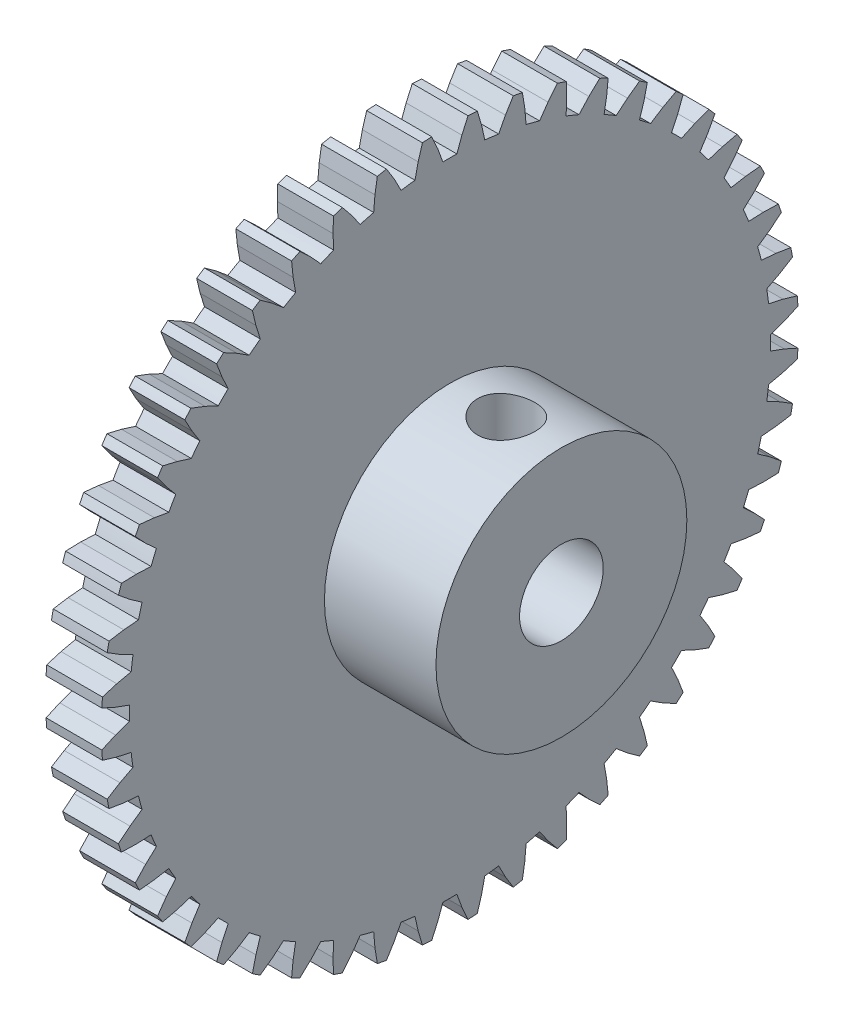
SolidWorks part; units mm, degrees
material "Plain Carbon Steel"
ref_plane "Front Plane" through (0, 0, 0) normal (0, 0, 1) x (1, 0, 0)
ref_plane "Top Plane" through (0, 0, 0) normal (0, 1, 0) x (1, 0, 0)
ref_plane "Right Plane" through (0, 0, 0) normal (1, 0, 0) x (0, 0, -1)
ref_plane "Plane1" through (2, 0, 0) normal (1, 0, 0) x (0, 0, -1)
sketch "Sketch1" plane through (2, 0, 0) normal (1, 0, 0) x (0, 0, -1)
  line L0 (-11.4973, -0.2509) -> (-11.9923, -0.431)
  line L1 (-11.9923, -0.431) -> (-12.483, -0.6512)
  line L2 (-12.4612, -0.9838) -> (-11.9459, -1.138)
  line L3 (-11.9459, -1.138) -> (-11.4316, -1.252)
  line L4 (-11.3662, -1.7494) -> (-11.8334, -1.9926)
  line L5 (-11.8334, -1.9926) -> (-12.2912, -2.2749)
  line L6 (-12.2262, -2.6019) -> (-11.6952, -2.6875)
  line L7 (-11.6952, -2.6875) -> (-11.1704, -2.7334)
  line L8 (-11.0406, -3.218) -> (-11.4721, -3.5202)
  line L9 (-11.4721, -3.5202) -> (-11.8891, -3.8598)
  line L10 (-11.782, -4.1755) -> (-11.2443, -4.191)
  line L11 (-11.2443, -4.191) -> (-10.7181, -4.168)
  line L12 (-10.5261, -4.6316) -> (-10.9145, -4.9875)
  line L13 (-10.9145, -4.9875) -> (-11.2836, -5.3786)
  line L14 (-11.1362, -5.6776) -> (-10.6011, -5.6228)
  line L15 (-10.6011, -5.6228) -> (-10.0824, -5.5314)
  line L16 (-9.8315, -5.9659) -> (-10.1701, -6.3694)
  line L17 (-10.1701, -6.3694) -> (-10.485, -6.8054)
  line L18 (-10.2999, -7.0826) -> (-9.7765, -6.9585)
  line L19 (-9.7765, -6.9585) -> (-9.2741, -6.8001)
  line L20 (-8.9687, -7.1981) -> (-9.2517, -7.6424)
  line L21 (-9.2517, -7.6424) -> (-9.5071, -8.1158)
  line L22 (-9.2873, -8.3664) -> (-8.7846, -8.175)
  line L23 (-8.7846, -8.175) -> (-8.3072, -7.9524)
  line L24 (-7.9524, -8.3072) -> (-8.175, -8.7846)
  line L25 (-8.175, -8.7846) -> (-8.3664, -9.2873)
  line L26 (-8.1158, -9.5071) -> (-7.6424, -9.2517)
  line L27 (-7.6424, -9.2517) -> (-7.1981, -8.9687)
  line L28 (-6.8001, -9.2741) -> (-6.9585, -9.7765)
  line L29 (-6.9585, -9.7765) -> (-7.0826, -10.2999)
  line L30 (-6.8054, -10.485) -> (-6.3694, -10.1701)
  line L31 (-6.3694, -10.1701) -> (-5.9659, -9.8315)
  line L32 (-5.5314, -10.0824) -> (-5.6228, -10.6011)
  line L33 (-5.6228, -10.6011) -> (-5.6776, -11.1362)
  line L34 (-5.3786, -11.2836) -> (-4.9875, -10.9145)
  line L35 (-4.9875, -10.9145) -> (-4.6316, -10.5261)
  line L36 (-4.168, -10.7181) -> (-4.191, -11.2443)
  line L37 (-4.191, -11.2443) -> (-4.1755, -11.782)
  line L38 (-3.8598, -11.8891) -> (-3.5202, -11.4721)
  line L39 (-3.5202, -11.4721) -> (-3.218, -11.0406)
  line L40 (-2.7334, -11.1704) -> (-2.6875, -11.6952)
  line L41 (-2.6875, -11.6952) -> (-2.6019, -12.2262)
  line L42 (-2.2749, -12.2912) -> (-1.9926, -11.8334)
  line L43 (-1.9926, -11.8334) -> (-1.7494, -11.3662)
  line L44 (-1.252, -11.4316) -> (-1.138, -11.9459)
  line L45 (-1.138, -11.9459) -> (-0.9838, -12.4612)
  line L46 (-0.6512, -12.483) -> (-0.431, -11.9923)
  line L47 (-0.431, -11.9923) -> (-0.2509, -11.4973)
  line L48 (0.2509, -11.4973) -> (0.431, -11.9923)
  line L49 (0.431, -11.9923) -> (0.6512, -12.483)
  line L50 (0.9838, -12.4612) -> (1.138, -11.9459)
  line L51 (1.138, -11.9459) -> (1.252, -11.4316)
  line L52 (1.7494, -11.3662) -> (1.9926, -11.8334)
  line L53 (1.9926, -11.8334) -> (2.2749, -12.2912)
  line L54 (2.6019, -12.2262) -> (2.6875, -11.6952)
  line L55 (2.6875, -11.6952) -> (2.7334, -11.1704)
  line L56 (3.218, -11.0406) -> (3.5202, -11.4721)
  line L57 (3.5202, -11.4721) -> (3.8598, -11.8891)
  line L58 (4.1755, -11.782) -> (4.191, -11.2443)
  line L59 (4.191, -11.2443) -> (4.168, -10.7181)
  line L60 (4.6316, -10.5261) -> (4.9875, -10.9145)
  line L61 (4.9875, -10.9145) -> (5.3786, -11.2836)
  line L62 (5.6776, -11.1362) -> (5.6228, -10.6011)
  line L63 (5.6228, -10.6011) -> (5.5314, -10.0824)
  line L64 (5.9659, -9.8315) -> (6.3694, -10.1701)
  line L65 (6.3694, -10.1701) -> (6.8054, -10.485)
  line L66 (7.0826, -10.2999) -> (6.9585, -9.7765)
  line L67 (6.9585, -9.7765) -> (6.8001, -9.2741)
  line L68 (7.1981, -8.9687) -> (7.6424, -9.2517)
  line L69 (7.6424, -9.2517) -> (8.1158, -9.5071)
  line L70 (8.3664, -9.2873) -> (8.175, -8.7846)
  line L71 (8.175, -8.7846) -> (7.9524, -8.3072)
  line L72 (8.3072, -7.9524) -> (8.7846, -8.175)
  line L73 (8.7846, -8.175) -> (9.2873, -8.3664)
  line L74 (9.5071, -8.1158) -> (9.2517, -7.6424)
  line L75 (9.2517, -7.6424) -> (8.9687, -7.1981)
  line L76 (9.2741, -6.8001) -> (9.7765, -6.9585)
  line L77 (9.7765, -6.9585) -> (10.2999, -7.0826)
  line L78 (10.485, -6.8054) -> (10.1701, -6.3694)
  line L79 (10.1701, -6.3694) -> (9.8315, -5.9659)
  line L80 (10.0824, -5.5314) -> (10.6011, -5.6228)
  line L81 (10.6011, -5.6228) -> (11.1362, -5.6776)
  line L82 (11.2836, -5.3786) -> (10.9145, -4.9875)
  line L83 (10.9145, -4.9875) -> (10.5261, -4.6316)
  line L84 (10.7181, -4.168) -> (11.2443, -4.191)
  line L85 (11.2443, -4.191) -> (11.782, -4.1755)
  line L86 (11.8891, -3.8598) -> (11.4721, -3.5202)
  line L87 (11.4721, -3.5202) -> (11.0406, -3.218)
  line L88 (11.1704, -2.7334) -> (11.6952, -2.6875)
  line L89 (11.6952, -2.6875) -> (12.2262, -2.6019)
  line L90 (12.2912, -2.2749) -> (11.8334, -1.9926)
  line L91 (11.8334, -1.9926) -> (11.3662, -1.7494)
  line L92 (11.4316, -1.252) -> (11.9459, -1.138)
  line L93 (11.9459, -1.138) -> (12.4612, -0.9838)
  line L94 (12.483, -0.6512) -> (11.9923, -0.431)
  line L95 (11.9923, -0.431) -> (11.4973, -0.2509)
  line L96 (11.4973, 0.2509) -> (11.9923, 0.431)
  line L97 (11.9923, 0.431) -> (12.483, 0.6512)
  line L98 (12.4612, 0.9838) -> (11.9459, 1.138)
  line L99 (11.9459, 1.138) -> (11.4316, 1.252)
  line L100 (11.3662, 1.7494) -> (11.8334, 1.9926)
  line L101 (11.8334, 1.9926) -> (12.2912, 2.2749)
  line L102 (12.2262, 2.6019) -> (11.6952, 2.6875)
  line L103 (11.6952, 2.6875) -> (11.1704, 2.7334)
  line L104 (11.0406, 3.218) -> (11.4721, 3.5202)
  line L105 (11.4721, 3.5202) -> (11.8891, 3.8598)
  line L106 (11.782, 4.1755) -> (11.2443, 4.191)
  line L107 (11.2443, 4.191) -> (10.7181, 4.168)
  line L108 (10.5261, 4.6316) -> (10.9145, 4.9875)
  line L109 (10.9145, 4.9875) -> (11.2836, 5.3786)
  line L110 (11.1362, 5.6776) -> (10.6011, 5.6228)
  line L111 (10.6011, 5.6228) -> (10.0824, 5.5314)
  line L112 (9.8315, 5.9659) -> (10.1701, 6.3694)
  line L113 (10.1701, 6.3694) -> (10.485, 6.8054)
  line L114 (10.2999, 7.0826) -> (9.7765, 6.9585)
  line L115 (9.7765, 6.9585) -> (9.2741, 6.8001)
  line L116 (8.9687, 7.1981) -> (9.2517, 7.6424)
  line L117 (9.2517, 7.6424) -> (9.5071, 8.1158)
  line L118 (9.2873, 8.3664) -> (8.7846, 8.175)
  line L119 (8.7846, 8.175) -> (8.3072, 7.9524)
  line L120 (7.9524, 8.3072) -> (8.175, 8.7846)
  line L121 (8.175, 8.7846) -> (8.3664, 9.2873)
  line L122 (8.1158, 9.5071) -> (7.6424, 9.2517)
  line L123 (7.6424, 9.2517) -> (7.1981, 8.9687)
  line L124 (6.8001, 9.2741) -> (6.9585, 9.7765)
  line L125 (6.9585, 9.7765) -> (7.0826, 10.2999)
  line L126 (6.8054, 10.485) -> (6.3694, 10.1701)
  line L127 (6.3694, 10.1701) -> (5.9659, 9.8315)
  line L128 (5.5314, 10.0824) -> (5.6228, 10.6011)
  line L129 (5.6228, 10.6011) -> (5.6776, 11.1362)
  line L130 (5.3786, 11.2836) -> (4.9875, 10.9145)
  line L131 (4.9875, 10.9145) -> (4.6316, 10.5261)
  line L132 (4.168, 10.7181) -> (4.191, 11.2443)
  line L133 (4.191, 11.2443) -> (4.1755, 11.782)
  line L134 (3.8598, 11.8891) -> (3.5202, 11.4721)
  line L135 (3.5202, 11.4721) -> (3.218, 11.0406)
  line L136 (2.7334, 11.1704) -> (2.6875, 11.6952)
  line L137 (2.6875, 11.6952) -> (2.6019, 12.2262)
  line L138 (2.2749, 12.2912) -> (1.9926, 11.8334)
  line L139 (1.9926, 11.8334) -> (1.7494, 11.3662)
  line L140 (1.252, 11.4316) -> (1.138, 11.9459)
  line L141 (1.138, 11.9459) -> (0.9838, 12.4612)
  line L142 (0.6512, 12.483) -> (0.431, 11.9923)
  line L143 (0.431, 11.9923) -> (0.2509, 11.4973)
  line L144 (-0.2509, 11.4973) -> (-0.431, 11.9923)
  line L145 (-0.431, 11.9923) -> (-0.6512, 12.483)
  line L146 (-0.9838, 12.4612) -> (-1.138, 11.9459)
  line L147 (-1.138, 11.9459) -> (-1.252, 11.4316)
  line L148 (-1.7494, 11.3662) -> (-1.9926, 11.8334)
  line L149 (-1.9926, 11.8334) -> (-2.2749, 12.2912)
  line L150 (-2.6019, 12.2262) -> (-2.6875, 11.6952)
  line L151 (-2.6875, 11.6952) -> (-2.7334, 11.1704)
  line L152 (-3.218, 11.0406) -> (-3.5202, 11.4721)
  line L153 (-3.5202, 11.4721) -> (-3.8598, 11.8891)
  line L154 (-4.1755, 11.782) -> (-4.191, 11.2443)
  line L155 (-4.191, 11.2443) -> (-4.168, 10.7181)
  line L156 (-4.6316, 10.5261) -> (-4.9875, 10.9145)
  line L157 (-4.9875, 10.9145) -> (-5.3786, 11.2836)
  line L158 (-5.6776, 11.1362) -> (-5.6228, 10.6011)
  line L159 (-5.6228, 10.6011) -> (-5.5314, 10.0824)
  line L160 (-5.9659, 9.8315) -> (-6.3694, 10.1701)
  line L161 (-6.3694, 10.1701) -> (-6.8054, 10.485)
  line L162 (-7.0826, 10.2999) -> (-6.9585, 9.7765)
  line L163 (-6.9585, 9.7765) -> (-6.8001, 9.2741)
  line L164 (-7.1981, 8.9687) -> (-7.6424, 9.2517)
  line L165 (-7.6424, 9.2517) -> (-8.1158, 9.5071)
  line L166 (-8.3664, 9.2873) -> (-8.175, 8.7846)
  line L167 (-8.175, 8.7846) -> (-7.9524, 8.3072)
  line L168 (-8.3072, 7.9524) -> (-8.7846, 8.175)
  line L169 (-8.7846, 8.175) -> (-9.2873, 8.3664)
  line L170 (-9.5071, 8.1158) -> (-9.2517, 7.6424)
  line L171 (-9.2517, 7.6424) -> (-8.9687, 7.1981)
  line L172 (-9.2741, 6.8001) -> (-9.7765, 6.9585)
  line L173 (-9.7765, 6.9585) -> (-10.2999, 7.0826)
  line L174 (-10.485, 6.8054) -> (-10.1701, 6.3694)
  line L175 (-10.1701, 6.3694) -> (-9.8315, 5.9659)
  line L176 (-10.0824, 5.5314) -> (-10.6011, 5.6228)
  line L177 (-10.6011, 5.6228) -> (-11.1362, 5.6776)
  line L178 (-11.2836, 5.3786) -> (-10.9145, 4.9875)
  line L179 (-10.9145, 4.9875) -> (-10.5261, 4.6316)
  line L180 (-10.7181, 4.168) -> (-11.2443, 4.191)
  line L181 (-11.2443, 4.191) -> (-11.782, 4.1755)
  line L182 (-11.8891, 3.8598) -> (-11.4721, 3.5202)
  line L183 (-11.4721, 3.5202) -> (-11.0406, 3.218)
  line L184 (-11.1704, 2.7334) -> (-11.6952, 2.6875)
  line L185 (-11.6952, 2.6875) -> (-12.2262, 2.6019)
  line L186 (-12.2912, 2.2749) -> (-11.8334, 1.9926)
  line L187 (-11.8334, 1.9926) -> (-11.3662, 1.7494)
  line L188 (-11.4316, 1.252) -> (-11.9459, 1.138)
  line L189 (-11.9459, 1.138) -> (-12.4612, 0.9838)
  line L190 (-12.483, 0.6512) -> (-11.9923, 0.431)
  line L191 (-11.9923, 0.431) -> (-11.4973, 0.2509)
  arc A0 (-12.483, -0.6512) -> (-12.4612, -0.9838) centre (0, 0) ccw
  arc A1 (-11.4316, -1.252) -> (-11.3662, -1.7494) centre (0, 0) ccw
  arc A2 (-12.2912, -2.2749) -> (-12.2262, -2.6019) centre (0, 0) ccw
  arc A3 (-11.1704, -2.7334) -> (-11.0406, -3.218) centre (0, 0) ccw
  arc A4 (-11.8891, -3.8598) -> (-11.782, -4.1755) centre (0, 0) ccw
  arc A5 (-10.7181, -4.168) -> (-10.5261, -4.6316) centre (0, 0) ccw
  arc A6 (-11.2836, -5.3786) -> (-11.1362, -5.6776) centre (0, 0) ccw
  arc A7 (-10.0824, -5.5314) -> (-9.8315, -5.9659) centre (0, 0) ccw
  arc A8 (-10.485, -6.8054) -> (-10.2999, -7.0826) centre (0, 0) ccw
  arc A9 (-9.2741, -6.8001) -> (-8.9687, -7.1981) centre (0, 0) ccw
  arc A10 (-9.5071, -8.1158) -> (-9.2873, -8.3664) centre (0, 0) ccw
  arc A11 (-8.3072, -7.9524) -> (-7.9524, -8.3072) centre (0, 0) ccw
  arc A12 (-8.3664, -9.2873) -> (-8.1158, -9.5071) centre (0, 0) ccw
  arc A13 (-7.1981, -8.9687) -> (-6.8001, -9.2741) centre (0, 0) ccw
  arc A14 (-7.0826, -10.2999) -> (-6.8054, -10.485) centre (0, 0) ccw
  arc A15 (-5.9659, -9.8315) -> (-5.5314, -10.0824) centre (0, 0) ccw
  arc A16 (-5.6776, -11.1362) -> (-5.3786, -11.2836) centre (0, 0) ccw
  arc A17 (-4.6316, -10.5261) -> (-4.168, -10.7181) centre (0, 0) ccw
  arc A18 (-4.1755, -11.782) -> (-3.8598, -11.8891) centre (0, 0) ccw
  arc A19 (-3.218, -11.0406) -> (-2.7334, -11.1704) centre (0, 0) ccw
  arc A20 (-2.6019, -12.2262) -> (-2.2749, -12.2912) centre (0, 0) ccw
  arc A21 (-1.7494, -11.3662) -> (-1.252, -11.4316) centre (0, 0) ccw
  arc A22 (-0.9838, -12.4612) -> (-0.6512, -12.483) centre (0, 0) ccw
  arc A23 (-0.2509, -11.4973) -> (0.2509, -11.4973) centre (0, 0) ccw
  arc A24 (0.6512, -12.483) -> (0.9838, -12.4612) centre (0, 0) ccw
  arc A25 (1.252, -11.4316) -> (1.7494, -11.3662) centre (0, 0) ccw
  arc A26 (2.2749, -12.2912) -> (2.6019, -12.2262) centre (0, 0) ccw
  arc A27 (2.7334, -11.1704) -> (3.218, -11.0406) centre (0, 0) ccw
  arc A28 (3.8598, -11.8891) -> (4.1755, -11.782) centre (0, 0) ccw
  arc A29 (4.168, -10.7181) -> (4.6316, -10.5261) centre (0, 0) ccw
  arc A30 (5.3786, -11.2836) -> (5.6776, -11.1362) centre (0, 0) ccw
  arc A31 (5.5314, -10.0824) -> (5.9659, -9.8315) centre (0, 0) ccw
  arc A32 (6.8054, -10.485) -> (7.0826, -10.2999) centre (0, 0) ccw
  arc A33 (6.8001, -9.2741) -> (7.1981, -8.9687) centre (0, 0) ccw
  arc A34 (8.1158, -9.5071) -> (8.3664, -9.2873) centre (0, 0) ccw
  arc A35 (7.9524, -8.3072) -> (8.3072, -7.9524) centre (0, 0) ccw
  arc A36 (9.2873, -8.3664) -> (9.5071, -8.1158) centre (0, 0) ccw
  arc A37 (8.9687, -7.1981) -> (9.2741, -6.8001) centre (0, 0) ccw
  arc A38 (10.2999, -7.0826) -> (10.485, -6.8054) centre (0, 0) ccw
  arc A39 (9.8315, -5.9659) -> (10.0824, -5.5314) centre (0, 0) ccw
  arc A40 (11.1362, -5.6776) -> (11.2836, -5.3786) centre (0, 0) ccw
  arc A41 (10.5261, -4.6316) -> (10.7181, -4.168) centre (0, 0) ccw
  arc A42 (11.782, -4.1755) -> (11.8891, -3.8598) centre (0, 0) ccw
  arc A43 (11.0406, -3.218) -> (11.1704, -2.7334) centre (0, 0) ccw
  arc A44 (12.2262, -2.6019) -> (12.2912, -2.2749) centre (0, 0) ccw
  arc A45 (11.3662, -1.7494) -> (11.4316, -1.252) centre (0, 0) ccw
  arc A46 (12.4612, -0.9838) -> (12.483, -0.6512) centre (0, 0) ccw
  arc A47 (11.4973, -0.2509) -> (11.4973, 0.2509) centre (0, 0) ccw
  arc A48 (12.483, 0.6512) -> (12.4612, 0.9838) centre (0, 0) ccw
  arc A49 (11.4316, 1.252) -> (11.3662, 1.7494) centre (0, 0) ccw
  arc A50 (12.2912, 2.2749) -> (12.2262, 2.6019) centre (0, 0) ccw
  arc A51 (11.1704, 2.7334) -> (11.0406, 3.218) centre (0, 0) ccw
  arc A52 (11.8891, 3.8598) -> (11.782, 4.1755) centre (0, 0) ccw
  arc A53 (10.7181, 4.168) -> (10.5261, 4.6316) centre (0, 0) ccw
  arc A54 (11.2836, 5.3786) -> (11.1362, 5.6776) centre (0, 0) ccw
  arc A55 (10.0824, 5.5314) -> (9.8315, 5.9659) centre (0, 0) ccw
  arc A56 (10.485, 6.8054) -> (10.2999, 7.0826) centre (0, 0) ccw
  arc A57 (9.2741, 6.8001) -> (8.9687, 7.1981) centre (0, 0) ccw
  arc A58 (9.5071, 8.1158) -> (9.2873, 8.3664) centre (0, 0) ccw
  arc A59 (8.3072, 7.9524) -> (7.9524, 8.3072) centre (0, 0) ccw
  arc A60 (8.3664, 9.2873) -> (8.1158, 9.5071) centre (0, 0) ccw
  arc A61 (7.1981, 8.9687) -> (6.8001, 9.2741) centre (0, 0) ccw
  arc A62 (7.0826, 10.2999) -> (6.8054, 10.485) centre (0, 0) ccw
  arc A63 (5.9659, 9.8315) -> (5.5314, 10.0824) centre (0, 0) ccw
  arc A64 (5.6776, 11.1362) -> (5.3786, 11.2836) centre (0, 0) ccw
  arc A65 (4.6316, 10.5261) -> (4.168, 10.7181) centre (0, 0) ccw
  arc A66 (4.1755, 11.782) -> (3.8598, 11.8891) centre (0, 0) ccw
  arc A67 (3.218, 11.0406) -> (2.7334, 11.1704) centre (0, 0) ccw
  arc A68 (2.6019, 12.2262) -> (2.2749, 12.2912) centre (0, 0) ccw
  arc A69 (1.7494, 11.3662) -> (1.252, 11.4316) centre (0, 0) ccw
  arc A70 (0.9838, 12.4612) -> (0.6512, 12.483) centre (0, 0) ccw
  arc A71 (0.2509, 11.4973) -> (-0.2509, 11.4973) centre (0, 0) ccw
  arc A72 (-0.6512, 12.483) -> (-0.9838, 12.4612) centre (0, 0) ccw
  arc A73 (-1.252, 11.4316) -> (-1.7494, 11.3662) centre (0, 0) ccw
  arc A74 (-2.2749, 12.2912) -> (-2.6019, 12.2262) centre (0, 0) ccw
  arc A75 (-2.7334, 11.1704) -> (-3.218, 11.0406) centre (0, 0) ccw
  arc A76 (-3.8598, 11.8891) -> (-4.1755, 11.782) centre (0, 0) ccw
  arc A77 (-4.168, 10.7181) -> (-4.6316, 10.5261) centre (0, 0) ccw
  arc A78 (-5.3786, 11.2836) -> (-5.6776, 11.1362) centre (0, 0) ccw
  arc A79 (-5.5314, 10.0824) -> (-5.9659, 9.8315) centre (0, 0) ccw
  arc A80 (-6.8054, 10.485) -> (-7.0826, 10.2999) centre (0, 0) ccw
  arc A81 (-6.8001, 9.2741) -> (-7.1981, 8.9687) centre (0, 0) ccw
  arc A82 (-8.1158, 9.5071) -> (-8.3664, 9.2873) centre (0, 0) ccw
  arc A83 (-7.9524, 8.3072) -> (-8.3072, 7.9524) centre (0, 0) ccw
  arc A84 (-9.2873, 8.3664) -> (-9.5071, 8.1158) centre (0, 0) ccw
  arc A85 (-8.9687, 7.1981) -> (-9.2741, 6.8001) centre (0, 0) ccw
  arc A86 (-10.2999, 7.0826) -> (-10.485, 6.8054) centre (0, 0) ccw
  arc A87 (-9.8315, 5.9659) -> (-10.0824, 5.5314) centre (0, 0) ccw
  arc A88 (-11.1362, 5.6776) -> (-11.2836, 5.3786) centre (0, 0) ccw
  arc A89 (-10.5261, 4.6316) -> (-10.7181, 4.168) centre (0, 0) ccw
  arc A90 (-11.782, 4.1755) -> (-11.8891, 3.8598) centre (0, 0) ccw
  arc A91 (-11.0406, 3.218) -> (-11.1704, 2.7334) centre (0, 0) ccw
  arc A92 (-12.2262, 2.6019) -> (-12.2912, 2.2749) centre (0, 0) ccw
  arc A93 (-11.3662, 1.7494) -> (-11.4316, 1.252) centre (0, 0) ccw
  arc A94 (-12.4612, 0.9838) -> (-12.483, 0.6512) centre (0, 0) ccw
  arc A95 (-11.4973, 0.2509) -> (-11.4973, -0.2509) centre (0, 0) ccw
extrude "Boss-Extrude1" add sketch "Sketch1" against normal blind 2
sketch "Sketch2" plane through (0, 0, 0) normal (0, 0, 1) x (1, 0, 0)
  line L0 (2, 4.5) -> (2, 0)
  line L1 (2, 0) -> (6, 0)
  line L2 (6, 0) -> (6, 4.5)
  line L3 (6, 4.5) -> (2, 4.5)
  line L4 (2, 0) -> (6, 0) construction
revolve "Revolve1" add sketch "Sketch2" angle 360 about L4
hole_wizard "Ø3.0 (3) Diameter Hole1" positions "Sketch4" profile "Sketch3" hole size "Ø3.0" standard "ANSI Metric"
sketch "Sketch4" plane through (6, 0, 0) normal (1, 0, 0) x (0, 0, -1)
  point P0 (0, 0)
sketch "Sketch3" plane through (6, 0, 0) normal (0, 1, 0) x (0, 0, -1)
  line L0 (0, 0) -> (0, 6)
  line L1 (0, 6) -> (1.5, 6)
  line L2 (1.5, 6) -> (1.5, 0)
  line L5 (1.5, 0) -> (0, 0)
  line L11 (0, -6.35) -> (0, 107.95) construction
  dimension "Thru Hole Dia." = 3
  dimension "Thru Hole Depth" = 6
ref_plane "Plane2" through (0, 1.0951, -0.0062) normal (0, -1, 0.0056) x (-1, 0, 0)
hole_wizard "Ø2.05 (2.05) Diameter Hole1" positions "Sketch6" profile "Sketch5" hole size "Ø2.05" standard "ANSI Metric"
sketch "Sketch6" plane through (0, 1.0951, -0.0062) normal (0, -1, 0.0056) x (-1, 0, 0)
  point P0 (-4, 0)
sketch "Sketch5" plane through (4, 1.0951, -0.0062) normal (1, 0, 0) x (0, -0.0056, -1)
  line L0 (0, 0) -> (0, 9)
  line L1 (0, 9) -> (1.025, 9)
  line L2 (1.025, 9) -> (1.025, 0)
  line L5 (1.025, 0) -> (0, 0)
  line L10 (0, 9) -> (-1.025, 9) construction
  line L11 (0, -6.35) -> (0, 107.95) construction
  dimension "Hole Dia." = 2.05
  dimension "Hole Depth" = 9
  dimension "Drill Angle" = 180
